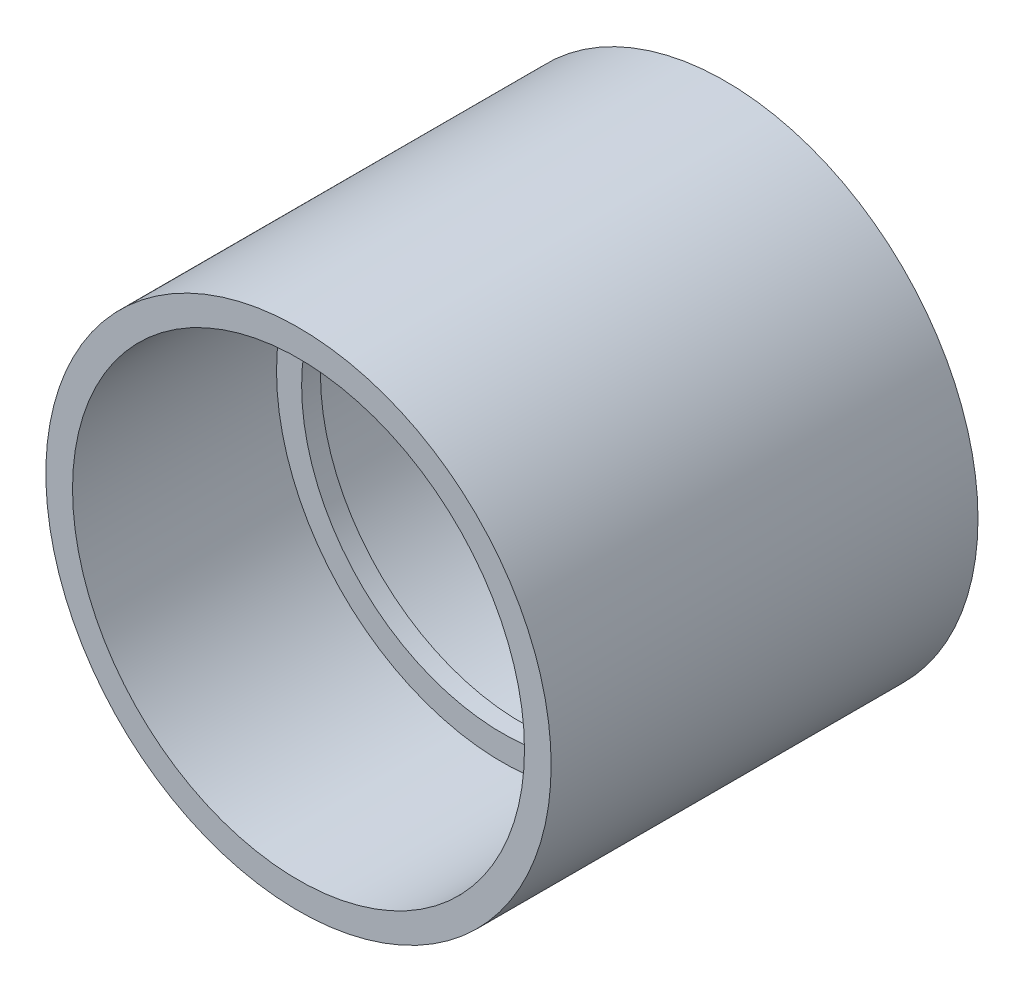
SolidWorks part; units mm, degrees
ref_plane "Front" through (0, 0, 0) normal (0, 0, 1) x (1, 0, 0)
ref_plane "Top" through (0, 0, 0) normal (0, 1, 0) x (1, 0, 0)
ref_plane "Right" through (0, 0, 0) normal (1, 0, 0) x (0, 0, -1)
sketch "Sketch2" plane through (0, 0, 0) normal (1, 0, 0) x (0, 0, -1)
  line L0 (-62.5946, 0) -> (53.5645, 0) construction
  line L1 (-53.975, 63.8969) -> (53.975, 63.8969)
  line L2 (53.975, 63.8969) -> (53.975, 57.15)
  line L3 (53.975, 57.15) -> (2.3813, 57.15)
  line L4 (2.3813, 57.15) -> (2.3813, 50.8)
  line L5 (2.3813, 50.8) -> (-2.3813, 50.8)
  line L6 (-2.3813, 50.8) -> (-2.3813, 57.15)
  line L7 (-2.3813, 57.15) -> (-53.975, 57.15)
  line L8 (-53.975, 57.15) -> (-53.975, 63.8969)
  point P6 (0, 63.8969)
  point P12 (0, 50.8)
  dimension "D1" = 107.95
  dimension "D2" = 127.7937
  dimension "D3" = 4.7625
  dimension "D4" = 114.3
  dimension "D5" = 101.6
revolve "Revolve1" add sketch "Sketch2" angle 360 about L0
